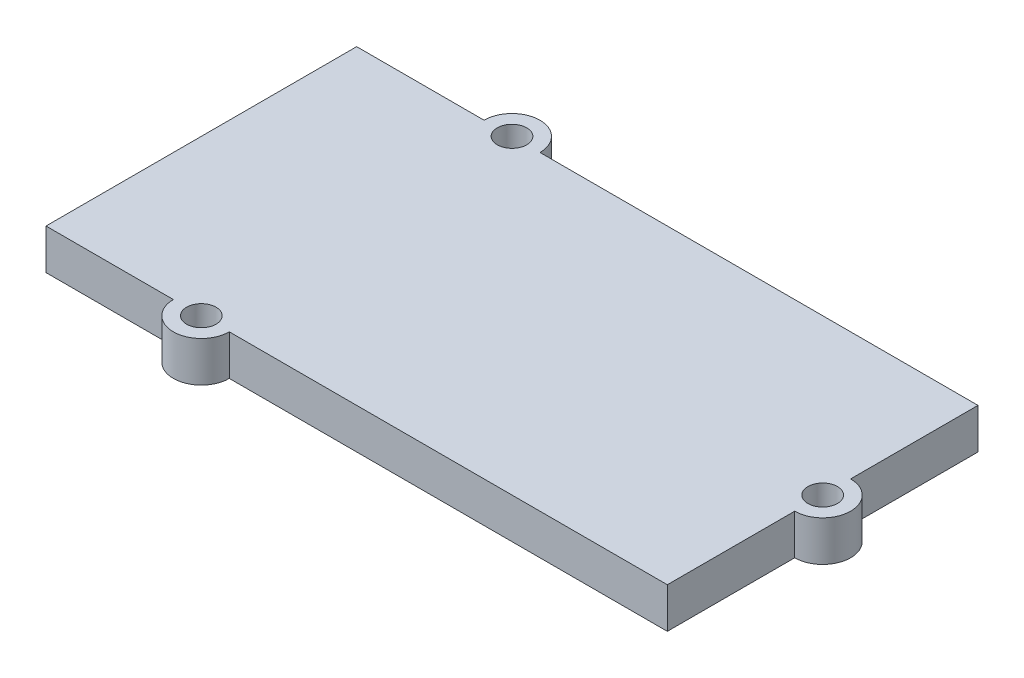
SolidWorks part; units mm, degrees
ref_plane "Front Plane" through (0, 0, 0) normal (0, 0, 1) x (1, 0, 0)
ref_plane "Top Plane" through (0, 0, 0) normal (0, 1, 0) x (1, 0, 0)
ref_plane "Right Plane" through (0, 0, 0) normal (1, 0, 0) x (0, 0, -1)
sketch "Sketch1" plane through (0, 0, 0) normal (0, 1, 0) x (1, 0, 0)
  line L0 (20, 0) -> (-20, 0)
  line L1 (-20, 0) -> (-20, -20)
  line L2 (-20, -10) -> (20, -10) construction
  line L3 (20, 0) -> (20, -20)
  line L4 (20, -20) -> (-20, -20)
  circle A0 centre (-10, 0) radius 0.95
  circle A1 centre (-10, -20) radius 0.95
  circle A2 centre (20, -10) radius 0.95
  circle A3 centre (20, -10) radius 1.8
  circle A4 centre (-10, 0) radius 1.8
  circle A5 centre (-10, -20) radius 1.8
  point P4 (0, 0)
  point P14 (0, -20)
  dimension "D2" = 1.9
  dimension "D5" = 1.9
  dimension "D1" = 40
  dimension "D3" = 10
  dimension "D4" = 10
  dimension "D6" = 0.85
  dimension "D7" = 0.85
extrude "Boss-Extrude1" add sketch "Sketch1" along normal blind 2.6 contours L2 L1 L4 A5 L3 A3 | A5 L4 A1 | A5 L4 A1 | L1 L2 A3 L3 L0 A4 | L0 A4 A0 | L0 A4 A0 | L3 A3 A2 | A3 L2 A2 L3 | L2 A3 L3 A2
